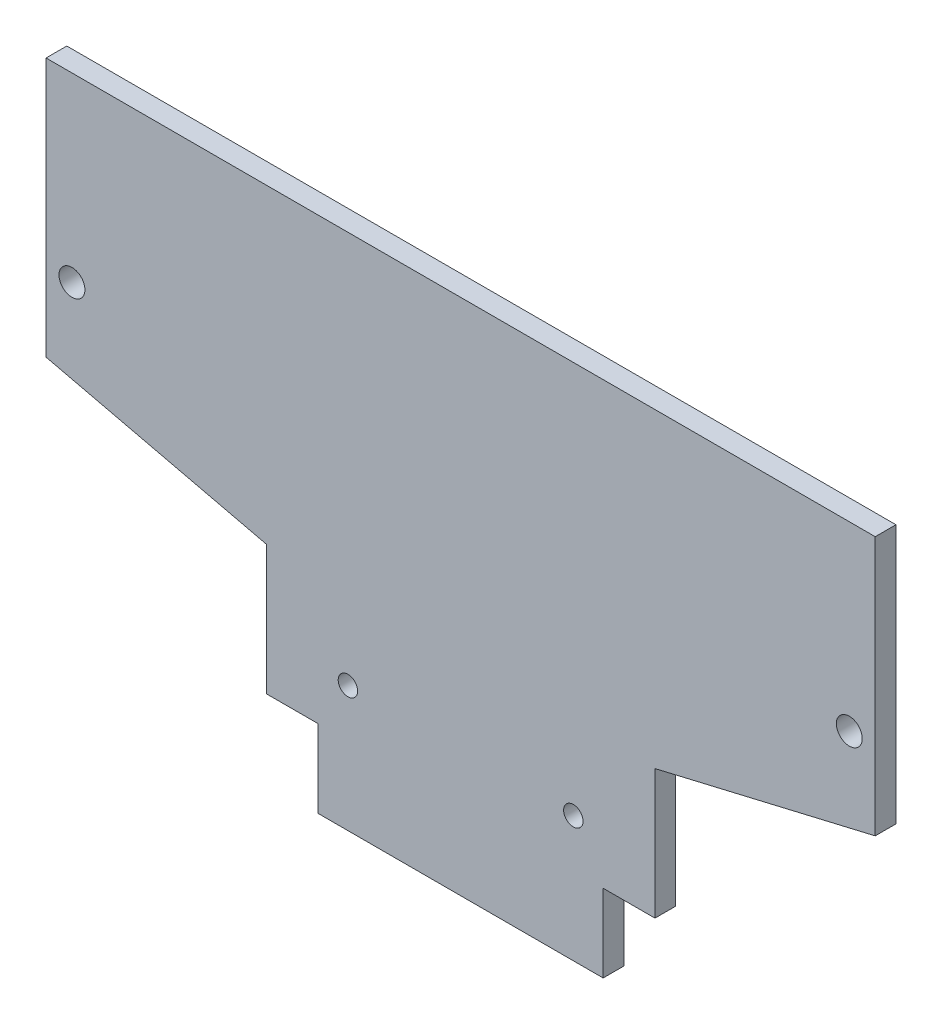
SolidWorks part; units mm, degrees
ref_plane "Front Plane" through (0, 0, 0) normal (0, 0, 1) x (1, 0, 0)
ref_plane "Top Plane" through (0, 0, 0) normal (0, 1, 0) x (1, 0, 0)
ref_plane "Right Plane" through (0, 0, 0) normal (1, 0, 0) x (0, 0, -1)
sketch "Sketch4" plane through (0, 0, 0) normal (0, 0, 1) x (1, 0, 0)
  line L0 (0, -66.3862) -> (0, 66.3862) construction
  line L1 (0, 40) -> (-32, 40)
  line L2 (-32, 40) -> (-32, 20)
  line L3 (-32, 20) -> (-15, 16)
  line L4 (-15, 16) -> (-15, 6)
  line L5 (-15, 6) -> (-11, 6)
  line L6 (-11, 6) -> (-11, 0)
  line L7 (-11, 0) -> (0, 0)
  line L8 (0, 0) -> (0, 40)
  circle A0 centre (-30, 26) radius 1
  circle A1 centre (-8.7, 9.7) radius 0.75
  point P3 (-13, 6)
  point P4 (0, 0)
  dimension "D10" = 2
  dimension "D13" = 1.5
  dimension "D1" = 32
  dimension "D2" = 4
  dimension "D3" = 15
  dimension "D4" = 6
  dimension "D5" = 10
  dimension "D6" = 20
  dimension "D7" = 40
  dimension "D8" = 26
  dimension "D9" = 30
  dimension "D11" = 9.7
  dimension "D12" = 6.3
extrude "Boss-Extrude1" add sketch "Sketch4" along normal blind 1.6
mirror "Mirror1" about plane through (0, 0, 1.6) normal (-1, 0, 0) of "Boss-Extrude1"
